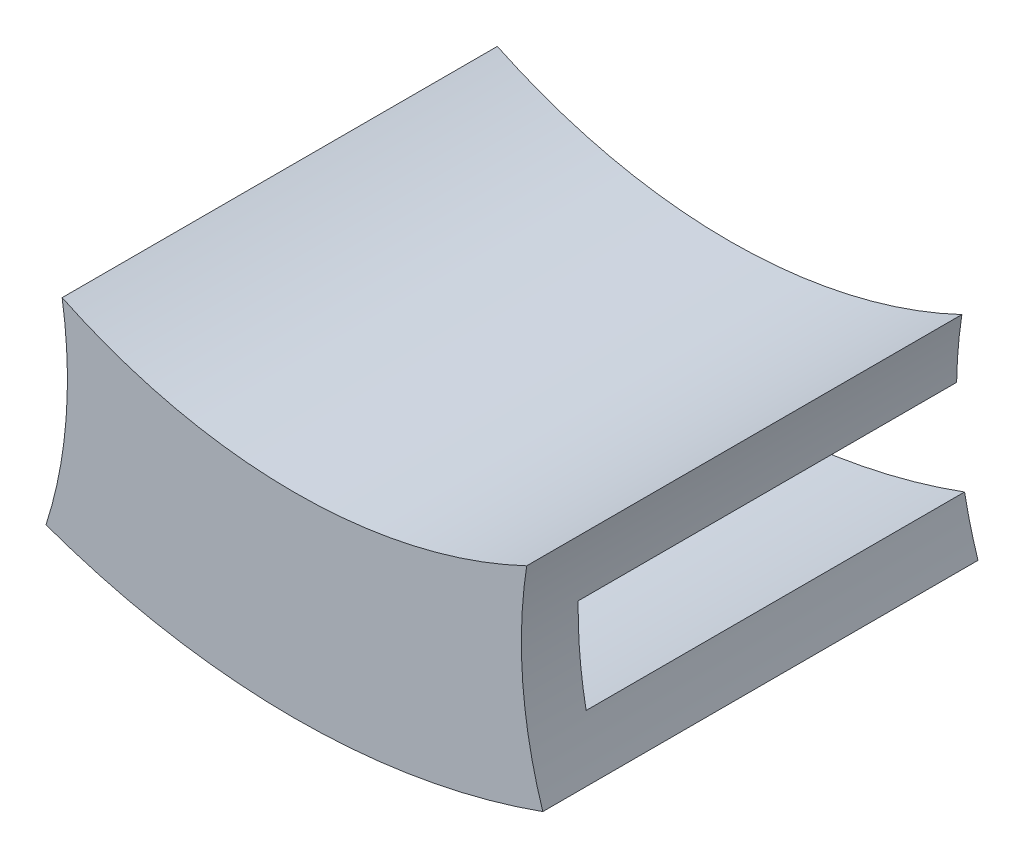
SolidWorks part; units mm, degrees
ref_plane "Front Plane" through (0, 0, 0) normal (0, 0, 1) x (1, 0, 0)
ref_plane "Top Plane" through (0, 0, 0) normal (0, 1, 0) x (1, 0, 0)
ref_plane "Right Plane" through (0, 0, 0) normal (1, 0, 0) x (0, 0, -1)
sketch "Sketch1" plane through (0, 0, 0) normal (0, 0, 1) x (1, 0, 0)
  arc A6 (12.2755, 39.1101) -> (13.1277, 28.286) centre (35.4954, 35.4928) ccw
  circle A7 centre (-35.4954, 35.4928) radius 23.5 construction
  arc A8 (-12.2753, 39.1089) -> (12.2755, 39.1101) centre (-0.0012, 64.8538) ccw
  circle A9 centre (35.4954, 35.4928) radius 23.5 construction
  arc A10 (-13.128, 28.2852) -> (13.1277, 28.286) centre (-0.0012, 64.8538) ccw
  arc A11 (-12.2753, 39.1089) -> (-13.128, 28.2852) centre (-35.4954, 35.4928) cw
extrude "Boss-Extrude1" add sketch "Sketch1" along normal blind 3
sketch "Sketch2" plane through (0, 0, 0) normal (0, 0, -1) x (-1, 0, 0)
  arc A0 (13.128, 28.2852) -> (12.4174, 31.0592) centre (35.4954, 35.4928) cw
  arc A1 (-0.0002, 33.4827) -> (11.9984, 35.8674) centre (0.0012, 64.8538) ccw
  arc A2 (12.2753, 39.1089) -> (13.128, 28.2852) centre (35.4954, 35.4928) ccw construction
  arc A3 (11.9984, 35.8674) -> (-11.9984, 35.8684) centre (0.0012, 64.8538) cw
  arc A4 (-13.1277, 28.286) -> (-12.2755, 39.1101) centre (-35.4954, 35.4928) ccw construction
  arc A5 (12.2753, 39.1089) -> (-12.2755, 39.1101) centre (0.0012, 64.8538) cw
  arc A6 (-17.0982, 20.871) -> (-34.8421, 12.0019) centre (-35.4954, 35.4928) ccw construction
  arc A7 (-11.9984, 35.8684) -> (-12.2755, 39.1101) centre (-35.4954, 35.4928) ccw
  arc A8 (11.9984, 35.8674) -> (12.2753, 39.1089) centre (35.4954, 35.4928) cw
  arc A11 (-13.1277, 28.286) -> (13.128, 28.2852) centre (0.0012, 64.8538) ccw
  arc A12 (12.4174, 31.0592) -> (-12.4172, 31.0601) centre (0.0012, 64.8538) cw
  arc A13 (-13.1277, 28.286) -> (-12.4172, 31.0601) centre (-35.4954, 35.4928) ccw
  arc M9 (13.128, 28.2852) -> (12.2753, 39.1089) centre (35.4954, 35.4928) cw
  arc M10 (12.2753, 39.1089) -> (-12.2755, 39.1101) centre (0.0012, 64.8538) cw
  arc M11 (-12.2755, 39.1101) -> (-13.1277, 28.286) centre (-35.4954, 35.4928) cw
  arc M12 (-13.1277, 28.286) -> (13.128, 28.2852) centre (0.0012, 64.8538) ccw
extrude "Boss-Extrude2" add sketch "Sketch2" along normal blind 20 contours A3 A1 M9 M10 M11 | A12 M9 M11 M12
